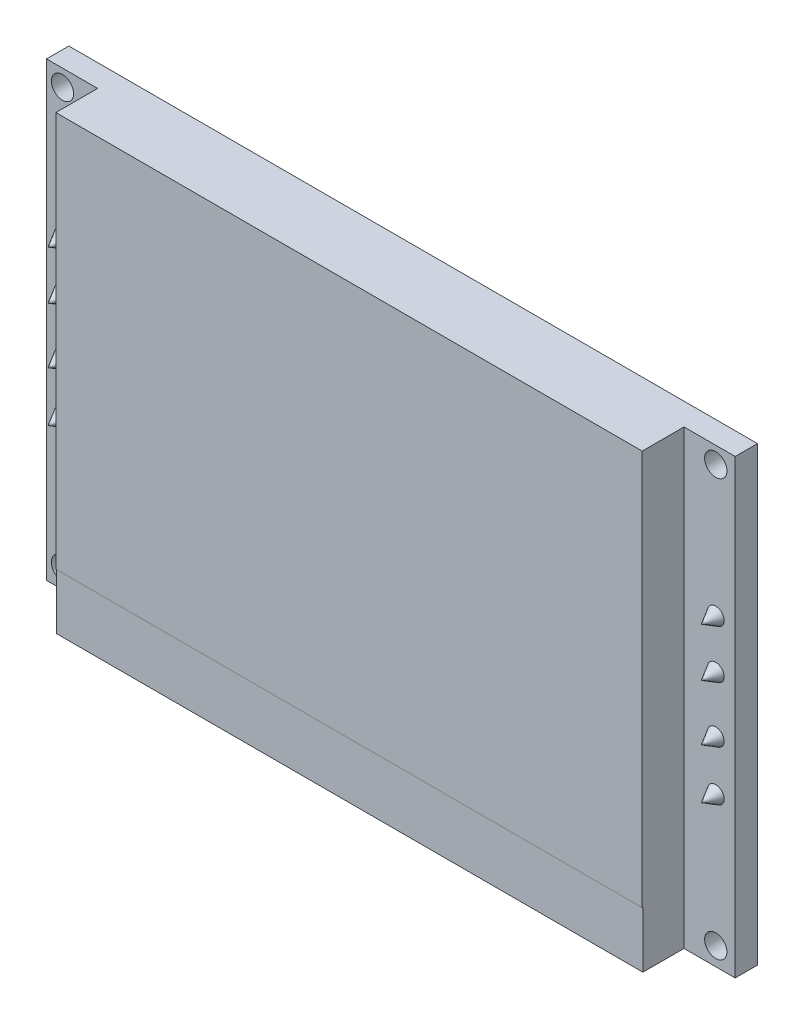
SolidWorks part; units mm, degrees
ref_plane "Plan de face" through (0, 0, 0) normal (0, 0, 1) x (1, 0, 0)
ref_plane "Plan de dessus" through (0, 0, 0) normal (0, 1, 0) x (1, 0, 0)
ref_plane "Plan de droite" through (0, 0, 0) normal (1, 0, 0) x (0, 0, -1)
sketch "Esquisse1" plane through (0, 0, 0) normal (0, 0, 1) x (1, 0, 0)
  line L1 (0, 0) -> (49.4, 0)
  line L2 (0, 0) -> (0, 32.4)
  line L3 (0, 32.4) -> (49.4, 32.4)
  line L4 (49.4, 0) -> (49.4, 32.4)
  dimension "D1" = 49.4
  dimension "D2" = 32.4
extrude "Boss.-Extru.1" add sketch "Esquisse1" along normal blind 1.6
sketch "Esquisse5" plane through (0, 0, 1.6) normal (0, 0, 1) x (1, 0, 0)
  line L0 (0, 32.4) -> (3.67, 32.4) construction
  line L1 (49.4, 32.4) -> (0, 32.4) construction
  line L2 (49.4, 32.4) -> (45.73, 32.4) construction
  line L4 (3.67, 32.4) -> (45.73, 32.4)
  line L5 (3.67, 32.4) -> (3.67, 0)
  line L6 (3.67, 0) -> (45.73, 0)
  line L7 (45.73, 32.4) -> (45.73, 0)
extrude "Boss.-Extru.2" add sketch "Esquisse5" along normal blind 3
sketch "Esquisse6" plane through (0, 0, 1.6) normal (0, 0, 1) x (1, 0, 0)
  circle A0 centre (1.1444, 31.2038) radius 0.8
  circle A1 centre (1.1444, 1.3139) radius 0.8
  circle A2 centre (48.0082, 1.3139) radius 0.8
  circle A3 centre (48.0082, 31.2038) radius 0.8
extrude "Enlèv. mat.-Extru.1" cut sketch "Esquisse6" against normal blind 3
sketch "Esquisse7" plane through (0, 0, 4.6) normal (0, 0, 1) x (1, 0, 0)
  line L0 (3.67, 32.4) -> (3.67, 0) construction
  line L1 (3.67, 4.0356) -> (45.73, 4.0356)
  line L2 (3.67, 4.0356) -> (3.67, 0)
  line L3 (3.67, 0) -> (45.73, 0)
  line L4 (45.73, 4.0356) -> (45.73, 0)
  line L5 (45.73, 0) -> (45.73, 32.4) construction
extrude "Enlèv. mat.-Extru.2" cut sketch "Esquisse7" against normal blind 0.05
sketch "Esquisse8" plane through (0, 0, 1.6) normal (0, 0, 1) x (1, 0, 0)
  line L0 (1.1444, 31.2038) -> (1.1444, 21.8038) construction
  line L1 (1.1444, 1.3139) -> (1.1444, 10.7139) construction
  line L2 (48.0082, 31.2038) -> (48.0082, 21.8038) construction
  line L3 (48.0082, 1.3139) -> (48.0082, 10.7139) construction
  line L4 (1.1444, 21.8038) -> (1.1444, 10.7139) construction
  line L5 (48.0082, 21.8038) -> (48.0082, 10.7139) construction
  circle A0 centre (1.1444, 21.8038) radius 0.6
  circle A1 centre (1.1444, 10.7139) radius 0.6
  circle A2 centre (48.0082, 21.8038) radius 0.6
  circle A3 centre (48.0082, 10.7139) radius 0.6
  circle A4 centre (1.1444, 18.3157) radius 0.6
  circle A5 centre (1.1444, 14.3059) radius 0.6
  circle A6 centre (48.0082, 18.3157) radius 0.6
  circle A7 centre (48.0082, 14.3059) radius 0.6
extrude "Boss.-Extru.3" add sketch "Esquisse8" along normal blind 1.2 draft 30
